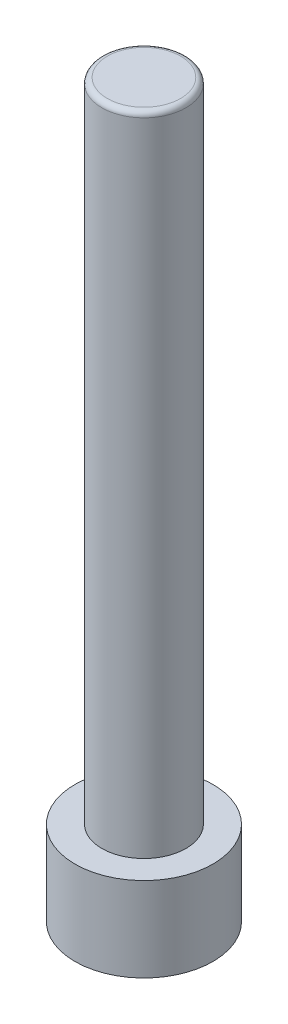
SolidWorks part; units mm, degrees
ref_plane "Front Plane" through (0, 0, 0) normal (0, 0, 1) x (1, 0, 0)
ref_plane "Top Plane" through (0, 0, 0) normal (0, 1, 0) x (1, 0, 0)
ref_plane "Right Plane" through (0, 0, 0) normal (1, 0, 0) x (0, 0, -1)
sketch "Sketch1" plane through (0, 0, 0) normal (0, 1, 0) x (1, 0, 0)
  line L1 (7.3901, 0) -> (3.695, 6.4) construction
  line L2 (3.695, 6.4) -> (-3.695, 6.4) construction
  line L3 (-3.695, 6.4) -> (-7.3901, 0) construction
  line L4 (-7.3901, 0) -> (-3.695, -6.4) construction
  line L5 (-3.695, -6.4) -> (3.695, -6.4) construction
  line L6 (3.695, -6.4) -> (7.3901, 0) construction
  circle A0 centre (0, 0) radius 6.4
  dimension "D1" = 12.8
extrude "Boss-Extrude1" add sketch "Sketch1" along normal blind 67.83
sketch "Sketch2" plane through (0, 67.83, 0) normal (0, 1, 0) x (1, 0, 0)
  circle A0 centre (0, 0) radius 3.9
  dimension "D1" = 7.8
extrude "Cut-Extrude1" cut sketch "Sketch2" against normal blind 60 flip side to cut
sketch "Sketch8" plane through (0, 0, 0) normal (0, -1, 0) x (1, 0, 0)
  line L1 (3.4641, 0) -> (1.7321, 3)
  line L2 (1.7321, 3) -> (-1.7321, 3)
  line L3 (-1.7321, 3) -> (-3.4641, 0)
  line L4 (-3.4641, 0) -> (-1.7321, -3)
  line L5 (-1.7321, -3) -> (1.7321, -3)
  line L6 (1.7321, -3) -> (3.4641, 0)
  circle A0 centre (0, 0) radius 3 construction
  dimension "D1" = 6
extrude "Cut-Extrude2" cut sketch "Sketch8" against normal blind 5.64
fillet "Fillet1" radius 0.5 1 edges at (0, 67.83, 3.9)
